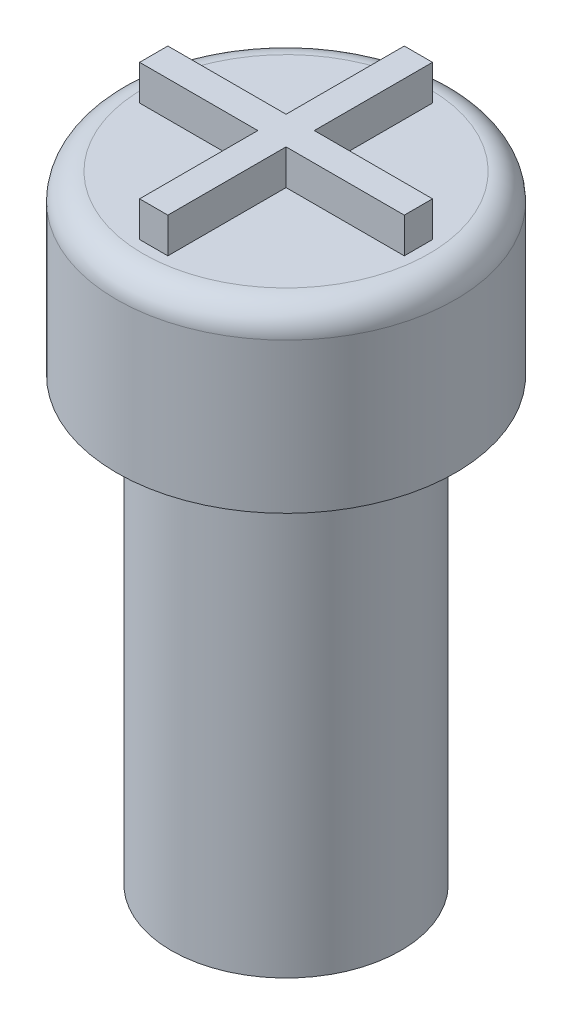
SolidWorks part; units mm, degrees
ref_plane "Front Plane" through (0, 0, 0) normal (0, 0, 1) x (1, 0, 0)
ref_plane "Top Plane" through (0, 0, 0) normal (0, 1, 0) x (1, 0, 0)
ref_plane "Right Plane" through (0, 0, 0) normal (1, 0, 0) x (0, 0, -1)
sketch "Sketch1" plane through (0, 0, 0) normal (0, 1, 0) x (1, 0, 0)
  circle A0 centre (0, 0) radius 3.25
  dimension "D1" = 6.5
extrude "Boss-Extrude1" add sketch "Sketch1" along normal blind 12.5 contours A0
sketch "Sketch2" plane through (0, 0, 0) normal (0, -1, 0) x (1, 0, 0)
  circle A1 centre (0, 0) radius 1.75
  dimension "D1" = 3.5
extrude "Cut-Extrude1" cut sketch "Sketch2" against normal blind 2.5
sketch "Sketch6" plane through (0, 12.5, 0) normal (0, 1, 0) x (1, 0, 0)
  circle A0 centre (0, 0) radius 4.8
  dimension "D1" = 9.6
extrude "Boss-Extrude2" add sketch "Sketch6" along normal blind 5 contours A0
sketch "Sketch7" plane through (0, 17.5, 0) normal (0, 1, 0) x (1, 0, 0)
  line L1 (-0.4, -3.75) -> (0.4, -3.75)
  line L2 (-0.4, -3.75) -> (-0.4, 3.75)
  line L3 (-0.4, 3.75) -> (0.4, 3.75)
  line L4 (0.4, -3.75) -> (0.4, 3.75)
  line L5 (-0.4, -3.75) -> (0.4, 3.75) construction
  line L6 (-0.4, 3.75) -> (0.4, -3.75) construction
  line L7 (-3.75, -0.4) -> (3.75, -0.4)
  line L8 (-3.75, -0.4) -> (-3.75, 0.4)
  line L9 (-3.75, 0.4) -> (3.75, 0.4)
  line L10 (3.75, -0.4) -> (3.75, 0.4)
  line L11 (-3.75, -0.4) -> (3.75, 0.4) construction
  line L12 (-3.75, 0.4) -> (3.75, -0.4) construction
  point P0 (0, 0)
  point P6 (0, 0)
  dimension "D1" = 0.8
  dimension "D2" = 7.5
  dimension "D3" = 7.5
  dimension "D4" = 0.8
sketch "Sketch8" plane through (0, 17.5, 0) normal (0, 1, 0) x (1, 0, 0)
  line L0 (0.4, 3.75) -> (-0.4, 3.75)
  line L1 (-0.4, 3.75) -> (-0.4, 0.4)
  line L2 (-0.4, -3.75) -> (-0.4, 3.75) construction
  line L3 (-3.75, 0.4) -> (3.75, 0.4) construction
  line L4 (-0.4, 0.4) -> (-3.75, 0.4)
  line L5 (-3.75, 0.4) -> (-3.75, -0.4)
  line L6 (-3.75, -0.4) -> (-0.4, -0.4)
  line L7 (-3.75, -0.4) -> (3.75, -0.4) construction
  line L8 (-0.4, -0.4) -> (-0.4, -3.75)
  line L9 (-0.4, -3.75) -> (0.4, -3.75)
  line L10 (0.4, -3.75) -> (0.4, -0.4)
  line L11 (0.4, -3.75) -> (0.4, 3.75) construction
  line L12 (0.4, -0.4) -> (3.75, -0.4)
  line L13 (3.75, -0.4) -> (3.75, 0.4)
  line L14 (3.75, 0.4) -> (0.4, 0.4)
  line L15 (0.4, 0.4) -> (0.4, 3.75)
extrude "Boss-Extrude3" add sketch "Sketch8" along normal blind 1
fillet "Fillet1" radius 0.75 1 edges at (0, 17.5, 4.8)
